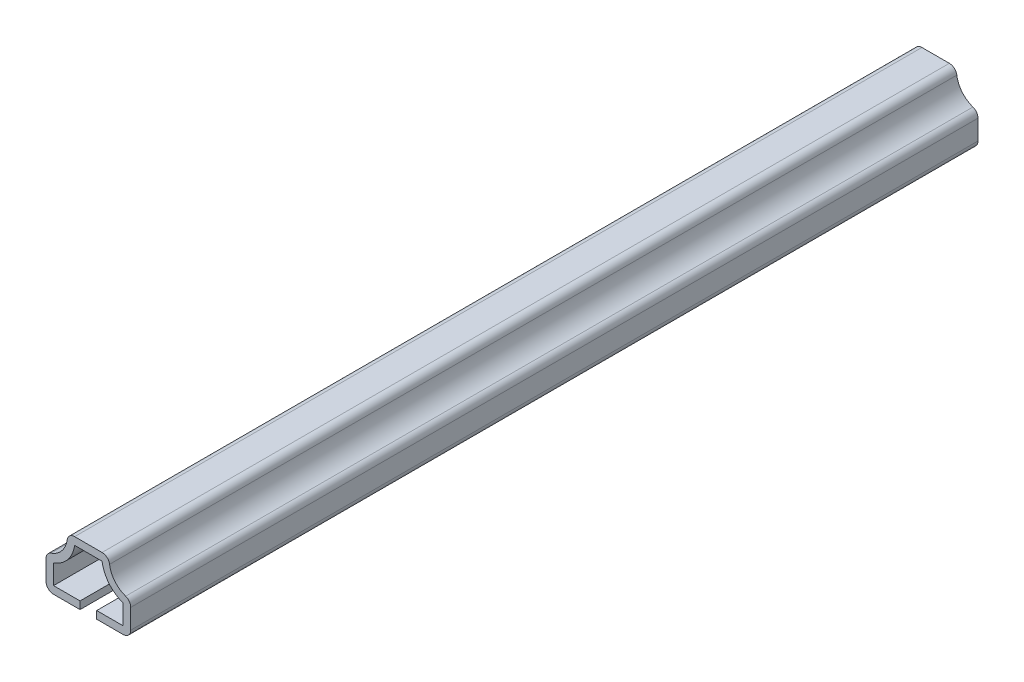
SolidWorks part; units mm, degrees
ref_plane "Front Plane" through (0, 0, 0) normal (0, 0, 1) x (1, 0, 0)
ref_plane "Top Plane" through (0, 0, 0) normal (0, 1, 0) x (1, 0, 0)
ref_plane "Right Plane" through (0, 0, 0) normal (1, 0, 0) x (0, 0, -1)
sketch "Sketch1" plane through (0, 0, 0) normal (0, 0, 1) x (1, 0, 0)
  line L0 (0, 0) -> (0, 15.875) construction
  line L1 (5.5562, 15.875) -> (-5.5562, 15.875)
  line L2 (-11.1125, 8.7312) -> (-11.1125, 0)
  line L3 (-11.1125, 0) -> (-2.1844, 0)
  line L4 (11.1125, 0) -> (2.1844, 0)
  line L5 (11.1125, 8.7312) -> (11.1125, 0)
  arc A0 (-5.5562, 15.875) -> (-11.1125, 8.7312) centre (-11.8509, 15.0382) cw
  arc A1 (5.5562, 15.875) -> (11.1125, 8.7312) centre (11.8509, 15.0382) ccw
extrude "Extrude-Thin1" add sketch "Sketch1" against normal blind 222.25 thin thin type one direction wall 1.9812
fillet "Fillet1" radius 1.9812 6 edges at (-11.1125, 8.7312, -111.125) (-11.1125, 0, -111.125) (11.1125, 0, -111.125) (11.1125, 8.7312, -111.125) (5.5562, 15.875, -111.125) (-5.5562, 15.875, -111.125)
equation "\"D1@Extrude-Thin1\"=\"D3@Sketch1\"*10"
